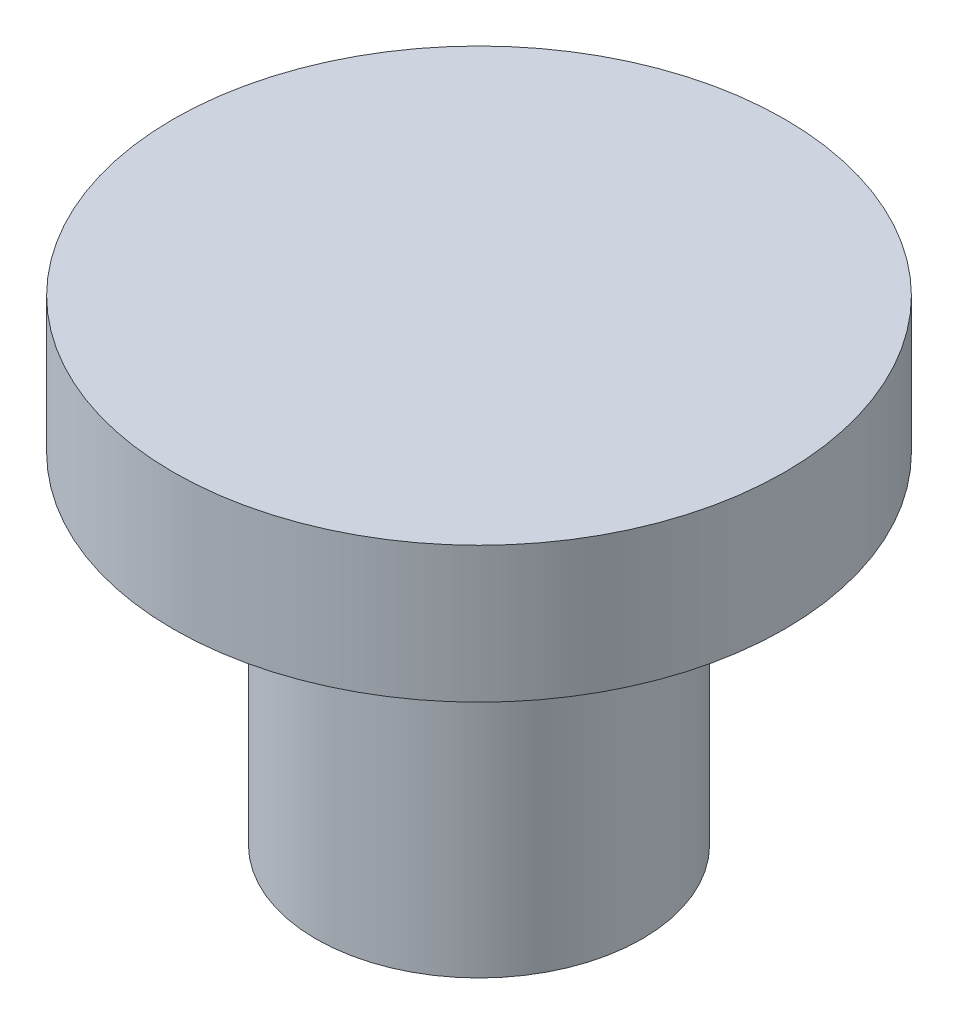
SolidWorks part; units mm, degrees
ref_plane "Front Plane" through (0, 0, 0) normal (0, 0, 1) x (1, 0, 0)
ref_plane "Top Plane" through (0, 0, 0) normal (0, 1, 0) x (1, 0, 0)
ref_plane "Right Plane" through (0, 0, 0) normal (1, 0, 0) x (0, 0, -1)
sketch "Sketch1" plane through (0, 0, 0) normal (0, 1, 0) x (1, 0, 0)
  circle A0 centre (0, 0) radius 3.048
  dimension "D1" = 6.096
extrude "Boss-Extrude1" add sketch "Sketch1" along normal blind 6.35
sketch "Sketch2" plane through (0, 6.35, 0) normal (0, 1, 0) x (1, 0, 0)
  circle A0 centre (0, 0) radius 5.715
  dimension "D1" = 11.43
extrude "Boss-Extrude2" add sketch "Sketch2" along normal blind 2.54
